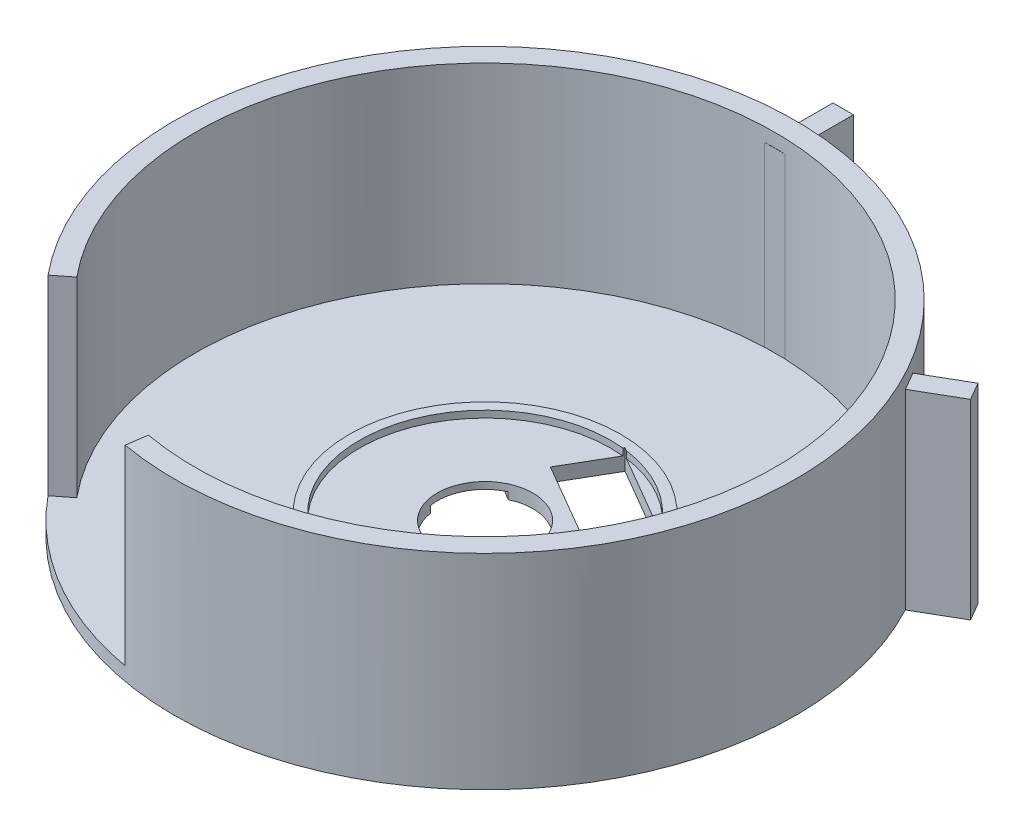
SolidWorks part; units mm, degrees
ref_plane "Front Plane" through (0, 0, 0) normal (0, 0, 1) x (1, 0, 0)
ref_plane "Top Plane" through (0, 0, 0) normal (0, 1, 0) x (1, 0, 0)
ref_plane "Right Plane" through (0, 0, 0) normal (1, 0, 0) x (0, 0, -1)
sketch "Sketch1" plane through (0, 0, 0) normal (0, 1, 0) x (1, 0, 0)
  circle A0 centre (0, 0) radius 45.5
  circle A1 centre (0, 0) radius 42.5
  dimension "D1" = 85
  dimension "D2" = 3
extrude "Boss-Extrude1" add sketch "Sketch1" along normal blind 30
sketch "Sketch2" plane through (0, 0, 0) normal (0, -1, 0) x (1, 0, 0)
  circle A0 centre (0, 0) radius 45.5
extrude "Boss-Extrude2" add sketch "Sketch2" against normal blind 2
sketch "Sketch3" plane through (0, 2, 0) normal (0, 1, 0) x (1, 0, 0)
  circle A0 centre (0, 0) radius 7
  dimension "D1" = 14
extrude "Cut-Extrude1" cut sketch "Sketch3" against normal blind 2
sketch "Sketch7" plane through (0, 2, 0) normal (0, 1, 0) x (1, 0, 0)
  line L12 (1.5, 52.4735) -> (1.5, 42.4735)
  line L13 (1.5, 52.4735) -> (-1.5, 52.4735)
  line L14 (-1.5, 52.4735) -> (-1.5, 42.4735)
  line L16 (46.1934, 24.9377) -> (37.5331, 19.9377)
  line L17 (46.1934, 24.9377) -> (44.6934, 27.5358)
  line L18 (44.6934, 27.5358) -> (36.0331, 22.5358)
  line L32 (-1.5, 42.4735) -> (1.5, 42.4735)
  line L37 (36.0331, 22.5358) -> (37.5331, 19.9377)
  circle A0 centre (0, 0) radius 42.5 construction
  point P27 (0, 0)
  dimension "D1" = 3
  dimension "D2" = 3
  dimension "D3" = 10
  dimension "D4" = 10
  dimension "D5" = 10
extrude "Boss-Extrude4" add sketch "Sketch7" along normal blind 26 and the other way blind 2
sketch "Sketch8" plane through (0, 2, 0) normal (0, 1, 0) x (1, 0, 0)
  circle A0 centre (0, 0) radius 19.8902
  circle A1 centre (0, 0) radius 18.3902
  dimension "D1" = 1.5
extrude "Boss-Extrude5" add sketch "Sketch8" along normal blind 1
sketch "Sketch10" plane through (0, 0, 0) normal (0, -1, 0) x (1, 0, 0)
  line L0 (0, -52.4735) -> (0, 8.0171) construction
  line L5 (1.5, -52.4735) -> (-1.5, -52.4735) construction
  line L8 (46.1934, -24.9377) -> (44.6934, -27.5358) construction
  line L24 (12.911, -7.4542) -> (45.4434, -26.2368) construction
  line L25 (2.0167, -18.4947) -> (14.9819, -10.9512)
  line L26 (2.0167, -18.4947) -> (-2.0065, -11.5799)
  line L27 (14.9819, -10.9512) -> (10.9587, -4.0365)
  line L28 (-2.0065, -11.5799) -> (10.9587, -4.0365)
  dimension "D1" = 15
  dimension "D2" = 8
  dimension "D3" = 9
extrude "Cut-Extrude4" cut sketch "Sketch10" against normal blind 5.5
sketch "Sketch11" plane through (0, 2, 0) normal (0, 1, 0) x (1, 0, 0)
  line L0 (0, 0) -> (-22.75, -39.4042) construction
  line L1 (-32.6066, -26.8741) -> (-35.1652, -28.8731)
  line L2 (-7.4952, -41.7388) -> (-7.926, -44.8043)
  line L5 (-35.1652, -28.8731) -> (-33.825, -37.7542)
  line L6 (-33.825, -37.7542) -> (-11.7383, -48.7724)
  line L7 (-11.7383, -48.7724) -> (-7.926, -44.8043)
  line L8 (-32.6066, -26.8741) -> (-25.9653, -26.8741)
  line L9 (-25.9653, -26.8741) -> (-9.9785, -35.4192)
  line L10 (-9.9785, -35.4192) -> (-7.4952, -41.7388)
  circle A0 centre (0, 0) radius 45.5 construction
  dimension "D1" = 22
  dimension "D2" = 22
extrude "Cut-Extrude5" cut sketch "Sketch11" along normal blind 58.5
sketch "Sketch12" plane through (0, 0, 0) normal (0, -1, 0) x (1, 0, 0)
  line L0 (-6.9123, 1.1048) -> (-24.2076, -9.4803)
  line L1 (-6.9123, 1.1048) -> (-2.5191, -6.0733)
  line L2 (-24.2076, -9.4803) -> (-19.8145, -16.6584)
  line L3 (-2.5191, -6.0733) -> (-19.8145, -16.6584)
  circle A0 centre (0, 0) radius 7 construction
extrude "Cut-Extrude6" cut sketch "Sketch12" against normal blind 1
